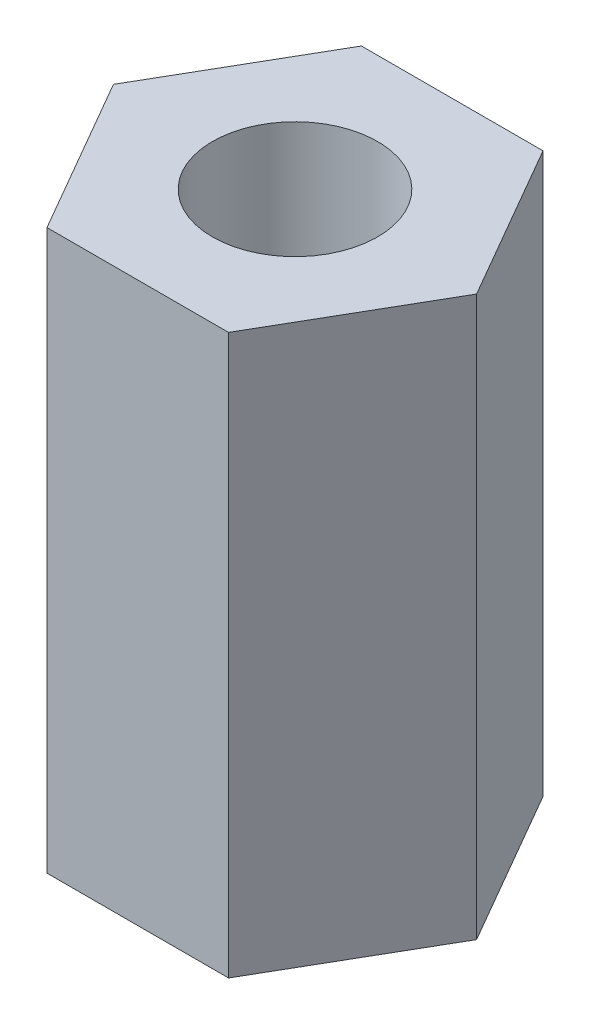
SolidWorks part; units mm, degrees
ref_plane "Front Plane" through (0, 0, 0) normal (0, 0, 1) x (1, 0, 0)
ref_plane "Top Plane" through (0, 0, 0) normal (0, 1, 0) x (1, 0, 0)
ref_plane "Right Plane" through (0, 0, 0) normal (1, 0, 0) x (0, 0, -1)
sketch "Sketch1" plane through (0, 0, 0) normal (0, 1, 0) x (1, 0, 0)
  line L1 (2.5981, 0) -> (1.299, 2.25)
  line L2 (1.299, 2.25) -> (-1.299, 2.25)
  line L3 (-1.299, 2.25) -> (-2.5981, 0)
  line L4 (-2.5981, 0) -> (-1.299, -2.25)
  line L5 (-1.299, -2.25) -> (1.299, -2.25)
  line L6 (1.299, -2.25) -> (2.5981, 0)
  circle A0 centre (0, 0) radius 2.25 construction
  circle A1 centre (0, 0) radius 1.1826
  dimension "D1" = 4.5
extrude "Boss-Extrude1" add sketch "Sketch1" along normal blind 8
